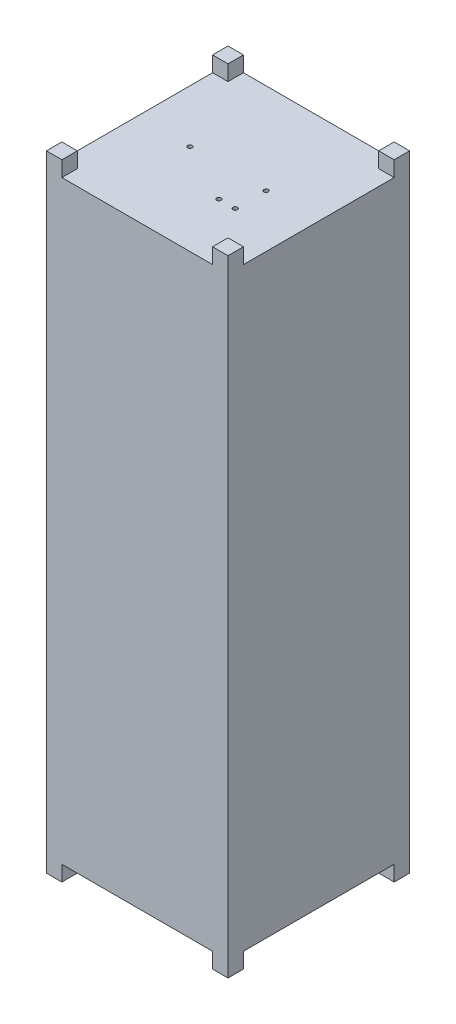
SolidWorks part; units mm, degrees
material "6061-O (SS)"
ref_plane "Front Plane" through (0, 0, 0) normal (0, 0, 1) x (1, 0, 0)
ref_plane "Top Plane" through (0, 0, 0) normal (0, 1, 0) x (1, 0, 0)
ref_plane "Right Plane" through (0, 0, 0) normal (1, 0, 0) x (0, 0, -1)
sketch "Sketch1" plane through (0, 0, 0) normal (0, 1, 0) x (1, 0, 0)
  line L1 (0, 0) -> (100, 0)
  line L2 (0, 0) -> (0, 100)
  line L3 (0, 100) -> (100, 100)
  line L4 (100, 0) -> (100, 100)
  line L8 (17, 100) -> (0, 100)
  line L9 (0, 83) -> (0, 100)
  line L14 (100, 83) -> (100, 100)
  line L15 (83, 100) -> (100, 100)
  line L16 (100, 0) -> (83, 0)
  line L21 (100, 17) -> (100, 0)
  line L22 (0, 0) -> (0, 17)
  line L27 (17, 0) -> (0, 0)
  dimension "D1" = 100
  dimension "D2" = 100
extrude "Boss-Extrude1" add sketch "Sketch1" against normal blind 327.5
sketch "Sketch30" plane through (0, 0, 0) normal (0, 1, 0) x (-1, 0, 0)
  line L3 (-100, 0) -> (0, 0) construction
  line L4 (-100, -100) -> (-100, 0) construction
  line L5 (-100, -100) -> (0, -100) construction
  line L6 (0, -100) -> (0, 0) construction
  circle A0 centre (-71, -50) radius 1.2
  circle A1 centre (-29, -50) radius 1.2
  circle A2 centre (-62, -33) radius 1.2
  circle A3 centre (-71, -33) radius 1.2
  dimension "D1" = 2.4
  dimension "D2" = 2.4
  dimension "D3" = 2.4
  dimension "D4" = 2.4
  dimension "D5" = 33
  dimension "D6" = 33
  dimension "D7" = 9
  dimension "D8" = 29
  dimension "D9" = 29
  dimension "D10" = 50
  dimension "D11" = 50
  dimension "D12" = 29
extrude "Cut-Extrude4" cut sketch "Sketch30" against normal blind 10
sketch "Sketch31" plane through (0, -327.5, 0) normal (0, -1, 0) x (-1, 0, 0)
  line L0 (-100, 0) -> (-100, 100) construction
  line L1 (0, 100) -> (-8.5, 100)
  line L2 (0, 100) -> (0, 91.5)
  line L3 (0, 91.5) -> (-8.5, 91.5)
  line L4 (-8.5, 100) -> (-8.5, 91.5)
  line L5 (-100, 100) -> (-91.5, 100)
  line L6 (-100, 100) -> (-100, 91.5)
  line L7 (-100, 91.5) -> (-91.5, 91.5)
  line L8 (-91.5, 100) -> (-91.5, 91.5)
  line L9 (0, 0) -> (-8.5, 0)
  line L10 (0, 0) -> (0, 8.5)
  line L11 (0, 8.5) -> (-8.5, 8.5)
  line L12 (-8.5, 0) -> (-8.5, 8.5)
  line L13 (-100, 0) -> (-91.5, 0)
  line L14 (-100, 0) -> (-100, 8.5)
  line L15 (-100, 8.5) -> (-91.5, 8.5)
  line L16 (-91.5, 0) -> (-91.5, 8.5)
  line L17 (0, 0) -> (0, 100) construction
  dimension "D1" = 8.5
  dimension "D2" = 8.5
  dimension "D3" = 8.5
  dimension "D4" = 8.5
  dimension "D5" = 8.5
  dimension "D6" = 8.5
extrude "Boss-Extrude2" add sketch "Sketch31" along normal blind 8.5 and the other way blind 336
